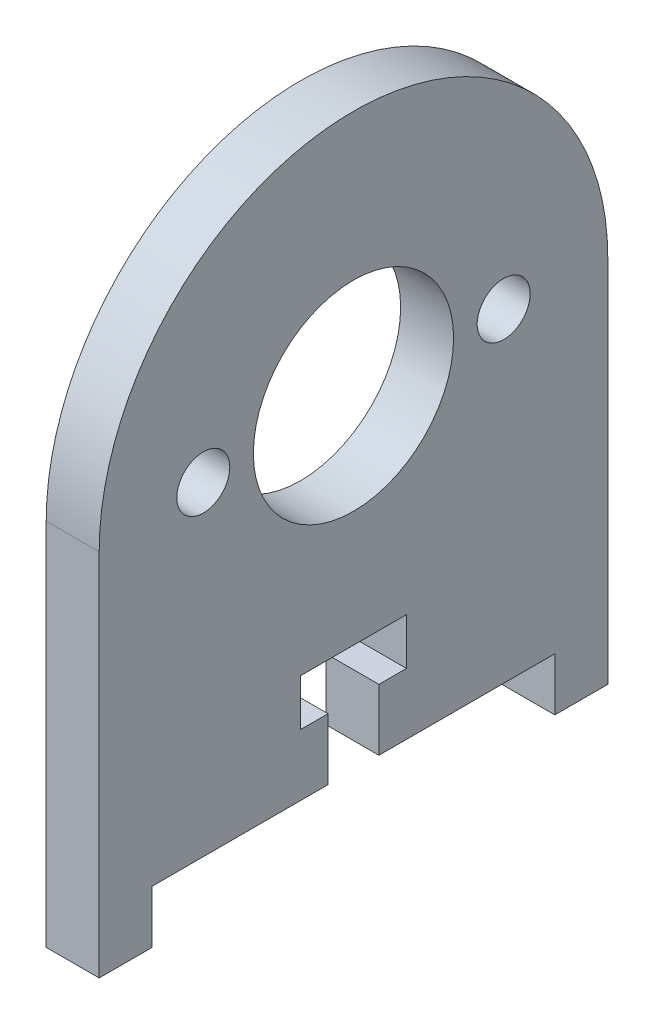
SolidWorks part; units mm, degrees
ref_plane "Front Plane" through (0, 0, 0) normal (0, 0, 1) x (1, 0, 0)
ref_plane "Top Plane" through (0, 0, 0) normal (0, 1, 0) x (1, 0, 0)
ref_plane "Right Plane" through (0, 0, 0) normal (1, 0, 0) x (0, 0, -1)
sketch "Sketch1" plane through (0, 0, 0) normal (1, 0, 0) x (0, 0, -1)
  line L0 (-13.716, -3.175) -> (-13.716, 18.9488)
  line L2 (16.764, 18.9488) -> (16.764, -3.175)
  line L3 (16.764, -3.175) -> (13.589, -3.175)
  line L4 (13.589, -3.175) -> (13.589, 0)
  line L5 (13.589, 0) -> (3.048, 0)
  line L6 (3.048, 0) -> (3.048, 3.683)
  line L7 (3.048, 3.683) -> (4.699, 3.683)
  line L8 (4.699, 3.683) -> (4.699, 6.477)
  line L9 (4.699, 6.477) -> (-1.651, 6.477)
  line L10 (-1.651, 6.477) -> (-1.651, 3.683)
  line L11 (-1.651, 3.683) -> (0, 3.683)
  line L12 (0, 3.683) -> (0, 0)
  line L13 (0, 0) -> (-10.541, 0)
  line L14 (-10.541, 0) -> (-10.541, -3.175)
  line L15 (-10.541, -3.175) -> (-13.716, -3.175)
  circle A1 centre (1.524, 19.424) radius 6
  circle A2 centre (1.524, 19.424) radius 12.5 construction
  circle A3 centre (1.524, 19.424) radius 9 construction
  arc A4 (-13.716, 18.9488) -> (16.764, 18.9488) centre (1.524, 18.9488) cw
  circle A5 centre (-7.476, 19.424) radius 1.5875
  circle A6 centre (10.524, 19.424) radius 1.5875
  point P26 (1.524, 6.477)
  dimension "D13" = 12
  dimension "D14" = 25
  dimension "D10" = 18
  dimension "D11" = 3.175
  dimension "D12" = 3.175
  dimension "D1" = 3.175
  dimension "D2" = 3.175
  dimension "D3" = 30.48
  dimension "D4" = 6.35
  dimension "D5" = 3.048
  dimension "D6" = 6.477
  dimension "D7" = 2.794
extrude "Boss-Extrude1" add sketch "Sketch1" along normal blind 3.175
